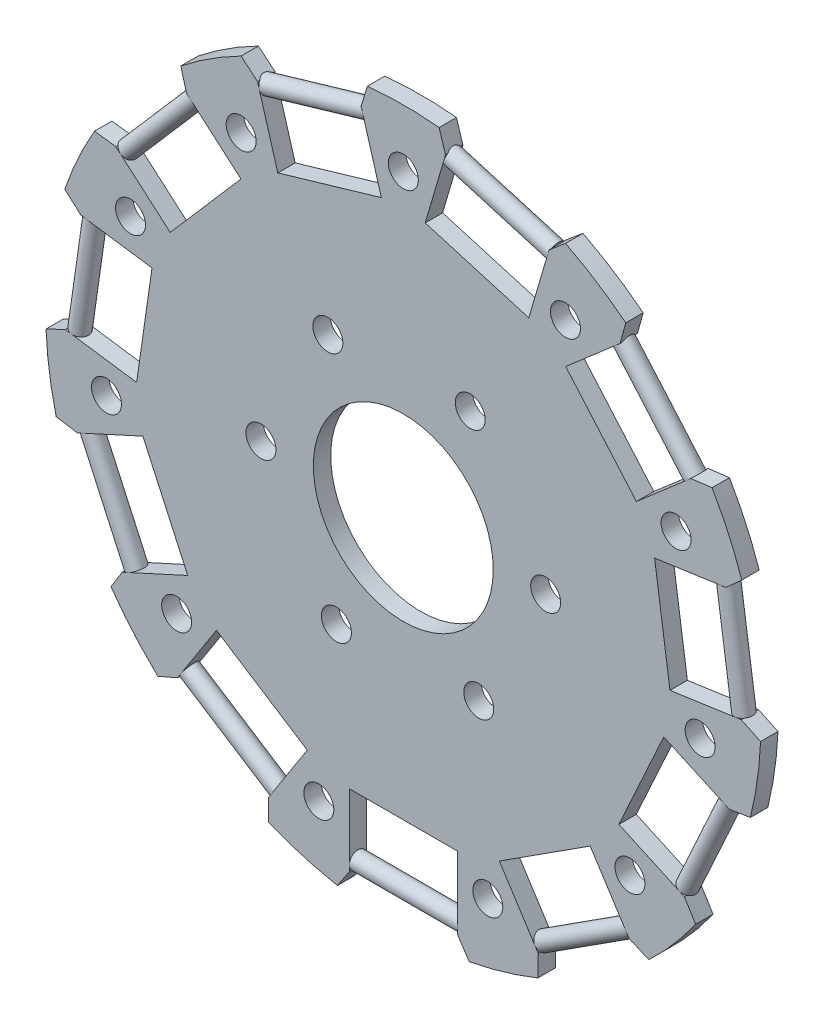
SolidWorks part; units mm, degrees
material "1060 Alloy"
ref_plane "Front Plane" through (0, 0, 0) normal (0, 0, 1) x (1, 0, 0)
ref_plane "Top Plane" through (0, 0, 0) normal (0, 1, 0) x (1, 0, 0)
ref_plane "Right Plane" through (0, 0, 0) normal (1, 0, 0) x (0, 0, -1)
sketch "Sketch1" plane through (0, 0, 0) normal (0, 0, 1) x (1, 0, 0)
  circle A0 centre (0, 0) radius 59.625
  circle A1 centre (0, 0) radius 15
  dimension "D1" = 119.25
  dimension "D2" = 30
extrude "Boss-Extrude1" add sketch "Sketch1" along normal blind 2.9
sketch "Sketch2" plane through (0, 0, 2.9) normal (0, 0, 1) x (1, 0, 0)
  circle A7 centre (0, 0) radius 50 construction
  circle A8 centre (0, 50) radius 2.5
  circle A9 centre (27.032, 42.0627) radius 2.5
  circle A10 centre (45.4816, 20.7708) radius 2.5
  circle A11 centre (49.4911, -7.1157) radius 2.5
  circle A12 centre (37.7875, -32.743) radius 2.5
  circle A13 centre (14.0866, -47.9746) radius 2.5
  circle A14 centre (-14.0866, -47.9746) radius 2.5
  circle A15 centre (-37.7875, -32.743) radius 2.5
  circle A16 centre (-49.4911, -7.1157) radius 2.5
  circle A17 centre (-45.4816, 20.7708) radius 2.5
  circle A18 centre (-27.032, 42.0627) radius 2.5
  dimension "D4" = 5
extrude "Cut-Extrude1" cut sketch "Sketch2" against normal blind 2.9
sketch "Sketch3" plane through (0, 0, 0) normal (0, 0, -1) x (-1, 0, 0)
  line L5 (50.9564, 32.2426) -> (39.1694, 45.8465)
  line L6 (39.1694, 45.8465) -> (37.1039, 46.7032)
  line L8 (27.077, 35.3691) -> (36.1463, 43.2271)
  line L11 (0, 0) -> (16.8002, 57.2092) construction
  line L12 (0, 0) -> (45.0629, 39.0445) construction
  line L13 (27.077, 35.3691) -> (38.8641, 21.7652)
  line L14 (0, 0) -> (54.236, -24.771) construction
  line L15 (0, 0) -> (32.234, -50.1608) construction
  line L16 (0, 0) -> (-0.002, -59.625) construction
  line L17 (0, 0) -> (-32.2374, -50.1586) construction
  line L18 (0, 0) -> (-54.2376, -24.7673) construction
  line L19 (0, 0) -> (-59.0178, 8.4875) construction
  line L20 (0, 0) -> (-45.0602, 39.0476) construction
  line L21 (0, 0) -> (-16.7964, 57.2103) construction
  line L22 (25.4356, 54.6733) -> (8.1649, 59.7451)
  line L23 (8.1649, 59.7451) -> (5.9642, 59.3491)
  line L24 (3.6567, 44.3933) -> (7.0378, 55.9072)
  line L25 (3.6567, 44.3933) -> (20.9274, 39.3216)
  line L26 (7.0378, 55.9072) -> (5.9642, 59.3491)
  line L27 (7.0378, 55.9072) -> (24.3085, 50.8354) construction
  line L28 (5.9642, 59.3491) -> (27.0728, 53.1503) construction
  line L29 (24.3085, 50.8354) -> (27.0728, 53.1503)
  line L30 (20.9274, 39.3216) -> (24.3085, 50.8354)
  line L31 (25.4356, 54.6733) -> (27.0728, 53.1503)
  line L32 (36.1463, 43.2271) -> (37.1039, 46.7032)
  line L33 (0, 0) -> (59.0184, 8.4835) construction
  line L34 (47.9333, 29.6233) -> (51.5103, 30.0762)
  line L35 (38.8641, 21.7652) -> (47.9333, 29.6233)
  line L36 (50.9564, 32.2426) -> (51.5103, 30.0762)
  line L37 (36.1463, 43.2271) -> (47.9333, 29.6233) construction
  line L38 (37.1039, 46.7032) -> (51.5103, 30.0762) construction
  line L39 (60.2989, -0.4249) -> (57.7379, 17.392)
  line L40 (57.7379, 17.392) -> (56.4635, 19.2293)
  line L41 (41.9006, 15.1155) -> (53.7786, 16.8228)
  line L42 (41.9006, 15.1155) -> (44.4617, -2.7014)
  line L43 (53.7786, 16.8228) -> (56.4635, 19.2293)
  line L44 (56.3396, -0.994) -> (59.5937, -2.5469)
  line L45 (44.4617, -2.7014) -> (56.3396, -0.994)
  line L46 (60.2989, -0.4249) -> (59.5937, -2.5469)
  line L47 (53.7786, 16.8228) -> (56.3396, -0.994) construction
  line L48 (56.4635, 19.2293) -> (59.5937, -2.5469) construction
  line L49 (50.497, -32.9575) -> (57.975, -16.5844)
  line L50 (57.975, -16.5844) -> (57.8963, -14.3497)
  line L51 (43.4211, -9.9373) -> (54.3365, -14.9226)
  line L52 (43.4211, -9.9373) -> (35.9431, -26.3104)
  line L53 (54.3365, -14.9226) -> (57.8963, -14.3497)
  line L54 (46.8585, -31.2957) -> (48.7564, -34.3613)
  line L55 (35.9431, -26.3104) -> (46.8585, -31.2957)
  line L56 (50.497, -32.9575) -> (48.7564, -34.3613)
  line L57 (54.3365, -14.9226) -> (46.8585, -31.2957) construction
  line L58 (57.8963, -14.3497) -> (48.7564, -34.3613) construction
  line L59 (24.6626, -55.0263) -> (39.8055, -45.2953)
  line L60 (39.8055, -45.2953) -> (40.9474, -43.3728)
  line L61 (31.1557, -31.835) -> (37.643, -41.9302)
  line L62 (31.1557, -31.835) -> (16.0128, -41.566)
  line L63 (37.643, -41.9302) -> (40.9474, -43.3728)
  line L64 (22.5001, -51.6613) -> (22.4394, -55.2663)
  line L65 (16.0128, -41.566) -> (22.5001, -51.6613)
  line L66 (24.6626, -55.0263) -> (22.4394, -55.2663)
  line L67 (37.643, -41.9302) -> (22.5001, -51.6613) construction
  line L68 (40.9474, -43.3728) -> (22.4394, -55.2663) construction
  line L69 (-9.002, -59.6247) -> (8.998, -59.6253)
  line L70 (8.998, -59.6253) -> (10.998, -58.6254)
  line L71 (8.9985, -43.6253) -> (8.9981, -55.6253)
  line L72 (8.9985, -43.6253) -> (-9.0015, -43.6247)
  line L73 (8.9981, -55.6253) -> (10.998, -58.6254)
  line L74 (-9.0019, -55.6247) -> (-11.002, -58.6246)
  line L75 (-9.0015, -43.6247) -> (-9.0019, -55.6247)
  line L76 (-9.002, -59.6247) -> (-11.002, -58.6246)
  line L77 (8.9981, -55.6253) -> (-9.0019, -55.6247) construction
  line L78 (10.998, -58.6254) -> (-11.002, -58.6246) construction
  line L79 (-39.8085, -45.2926) -> (-24.6663, -55.0247)
  line L80 (-24.6663, -55.0247) -> (-22.4432, -55.2648)
  line L81 (-16.0156, -41.5649) -> (-22.5036, -51.6597)
  line L82 (-16.0156, -41.5649) -> (-31.1578, -31.8329)
  line L83 (-22.5036, -51.6597) -> (-22.4432, -55.2648)
  line L84 (-37.6458, -41.9277) -> (-40.9503, -43.37)
  line L85 (-31.1578, -31.8329) -> (-37.6458, -41.9277)
  line L86 (-39.8085, -45.2926) -> (-40.9503, -43.37)
  line L87 (-22.5036, -51.6597) -> (-37.6458, -41.9277) construction
  line L88 (-22.4432, -55.2648) -> (-40.9503, -43.37) construction
  line L89 (-57.9761, -16.5805) -> (-50.4992, -32.9541)
  line L90 (-50.4992, -32.9541) -> (-48.7588, -34.358)
  line L91 (-35.9449, -26.3079) -> (-46.8606, -31.2926)
  line L92 (-35.9449, -26.3079) -> (-43.4218, -9.9343)
  line L93 (-46.8606, -31.2926) -> (-48.7588, -34.358)
  line L94 (-54.3375, -14.9189) -> (-57.8972, -14.3458)
  line L95 (-43.4218, -9.9343) -> (-54.3375, -14.9189)
  line L96 (-57.9761, -16.5805) -> (-57.8972, -14.3458)
  line L97 (-46.8606, -31.2926) -> (-54.3375, -14.9189) construction
  line L98 (-48.7588, -34.358) -> (-57.8972, -14.3458) construction
  line L99 (-57.7367, 17.3959) -> (-60.299, -0.4208)
  line L100 (-60.299, -0.4208) -> (-59.5938, -2.5428)
  line L101 (-44.4619, -2.6984) -> (-56.3397, -0.9902)
  line L102 (-44.4619, -2.6984) -> (-41.8996, 15.1183)
  line L103 (-56.3397, -0.9902) -> (-59.5938, -2.5428)
  line L104 (-53.7774, 16.8265) -> (-56.4622, 19.2332)
  line L105 (-41.8996, 15.1183) -> (-53.7774, 16.8265)
  line L106 (-57.7367, 17.3959) -> (-56.4622, 19.2332)
  line L107 (-56.3397, -0.9902) -> (-53.7774, 16.8265) construction
  line L108 (-59.5938, -2.5428) -> (-56.4622, 19.2332) construction
  line L109 (-39.1663, 45.8491) -> (-50.9542, 32.2461)
  line L110 (-50.9542, 32.2461) -> (-51.5083, 30.0797)
  line L111 (-38.8626, 21.7679) -> (-47.9313, 29.6265)
  line L112 (-38.8626, 21.7679) -> (-27.0746, 35.371)
  line L113 (-47.9313, 29.6265) -> (-51.5083, 30.0797)
  line L114 (-36.1434, 43.2296) -> (-37.1008, 46.7057)
  line L115 (-27.0746, 35.371) -> (-36.1434, 43.2296)
  line L116 (-39.1663, 45.8491) -> (-37.1008, 46.7057)
  line L117 (-47.9313, 29.6265) -> (-36.1434, 43.2296) construction
  line L118 (-51.5083, 30.0797) -> (-37.1008, 46.7057) construction
  line L119 (-8.1608, 59.7456) -> (-25.4319, 54.675)
  line L120 (-25.4319, 54.675) -> (-27.0692, 53.1521)
  line L121 (-20.9247, 39.323) -> (-24.3051, 50.837)
  line L122 (-20.9247, 39.323) -> (-3.6536, 44.3936)
  line L123 (-24.3051, 50.837) -> (-27.0692, 53.1521)
  line L124 (-7.034, 55.9076) -> (-5.9601, 59.3495)
  line L125 (-3.6536, 44.3936) -> (-7.034, 55.9076)
  line L126 (-8.1608, 59.7456) -> (-5.9601, 59.3495)
  line L127 (-24.3051, 50.837) -> (-7.034, 55.9076) construction
  line L128 (-27.0692, 53.1521) -> (-5.9601, 59.3495) construction
  circle A0 centre (0, 0) radius 59.625 construction
  point P3 (27.032, 42.0627)
  point P4 (45.4816, 20.7708)
  point P16 (0, 50)
  point P17 (27.032, 42.0627)
  point P29 (0, 0)
  point P38 (16.5185, 56.2497)
  point P40 (15.6732, 53.3713)
  point P41 (12.292, 41.8575)
  point P42 (27.0349, 42.0608)
  point P43 (44.3071, 38.3897)
  point P46 (42.0398, 36.4252)
  point P47 (32.9705, 28.5672)
  point P48 (45.483, 20.7677)
  point P49 (45.4816, 20.7708)
  point P50 (49.4911, -7.1157)
  point P58 (58.0286, 8.3412)
  point P60 (55.0591, 7.9144)
  point P61 (43.1812, 6.207)
  point P62 (49.4906, -7.1191)
  point P63 (49.4911, -7.1157)
  point P64 (37.7875, -32.743)
  point P72 (53.3263, -24.3555)
  point P74 (50.5975, -23.1092)
  point P75 (39.6821, -18.1238)
  point P76 (37.7853, -32.7456)
  point P77 (37.7875, -32.743)
  point P78 (14.0866, -47.9746)
  point P86 (31.6934, -49.3196)
  point P88 (30.0716, -46.7957)
  point P89 (23.5842, -36.7005)
  point P90 (14.0834, -47.9756)
  point P91 (14.0866, -47.9746)
  point P92 (-14.0866, -47.9746)
  point P100 (-0.002, -58.625)
  point P102 (-0.0019, -55.625)
  point P103 (-0.0015, -43.625)
  point P104 (-14.0899, -47.9737)
  point P105 (-14.0866, -47.9746)
  point P106 (-37.7875, -32.743)
  point P114 (-31.6967, -49.3174)
  point P116 (-30.0747, -46.7937)
  point P117 (-23.5867, -36.6989)
  point P118 (-37.7897, -32.7405)
  point P119 (-37.7875, -32.743)
  point P120 (-49.4911, -7.1157)
  point P128 (-53.328, -24.3519)
  point P130 (-50.5991, -23.1057)
  point P131 (-39.6833, -18.1211)
  point P132 (-49.4916, -7.1124)
  point P133 (-49.4911, -7.1157)
  point P134 (-45.4816, 20.7708)
  point P142 (-58.028, 8.3452)
  point P144 (-55.0585, 7.9181)
  point P145 (-43.1807, 6.2099)
  point P146 (-45.4802, 20.7738)
  point P147 (-45.4816, 20.7708)
  point P148 (-27.032, 42.0627)
  point P156 (-44.3045, 38.3927)
  point P158 (-42.0373, 36.4281)
  point P159 (-32.9686, 28.5694)
  point P160 (-27.0292, 42.0645)
  point P161 (-27.032, 42.0627)
  point P162 (0, 50)
  point P170 (-16.5147, 56.2508)
  point P172 (-15.6696, 53.3723)
  point P173 (-12.2892, 41.8583)
  point P174 (0.0034, 50)
  point P175 (0, 0)
  dimension "D7" = 11
  dimension "D8" = 14.085
  dimension "D9" = 9
  dimension "D10" = 9
  dimension "D11" = 2
  dimension "D12" = 12
  dimension "D13" = 3
  dimension "D14" = 90
  dimension "D15" = 1
extrude "Cut-Extrude2" cut sketch "Sketch3" against normal blind 2.9
sketch "Sketch4" plane through (8.6354, 2.5359, 0) normal (-0.9595, -0.2818, 0) x (0, 0, 1)
  line L0 (2.9, 51.6605) -> (2.9, 41.5655) construction
  line L1 (0, 51.6605) -> (0, 41.5655) construction
  line L2 (2.9, 43.625) -> (0, 43.625) construction
  circle A0 centre (1.45, 54.625) radius 1.45
  dimension "D1" = 11
extrude "Boss-Extrude2" add sketch "Sketch4" along normal blind 19
pattern_circular "CirPattern1" count 11 over 360 about axis through (0, 0, 0) along (0, 0, 1) of "Boss-Extrude2"
sketch "Sketch6" plane through (0, 0, 2.9) normal (0, 0, 1) x (1, 0, 0)
  line L0 (20.9247, 39.323) -> (0, 0) construction
  circle A0 centre (0, 0) radius 23.75 construction
  circle A1 centre (11.1567, 20.9664) radius 2.5
  circle A2 centre (23.7358, 0.8212) radius 2.5
  circle A3 centre (12.5791, -20.1452) radius 2.5
  circle A4 centre (-11.1567, -20.9664) radius 2.5
  circle A5 centre (-23.7358, -0.8212) radius 2.5
  circle A6 centre (-12.5791, 20.1452) radius 2.5
  point P20 (0, 0)
  dimension "D1" = 47.5
  dimension "D2" = 5
extrude "Cut-Extrude3" cut sketch "Sketch6" against normal blind 17
